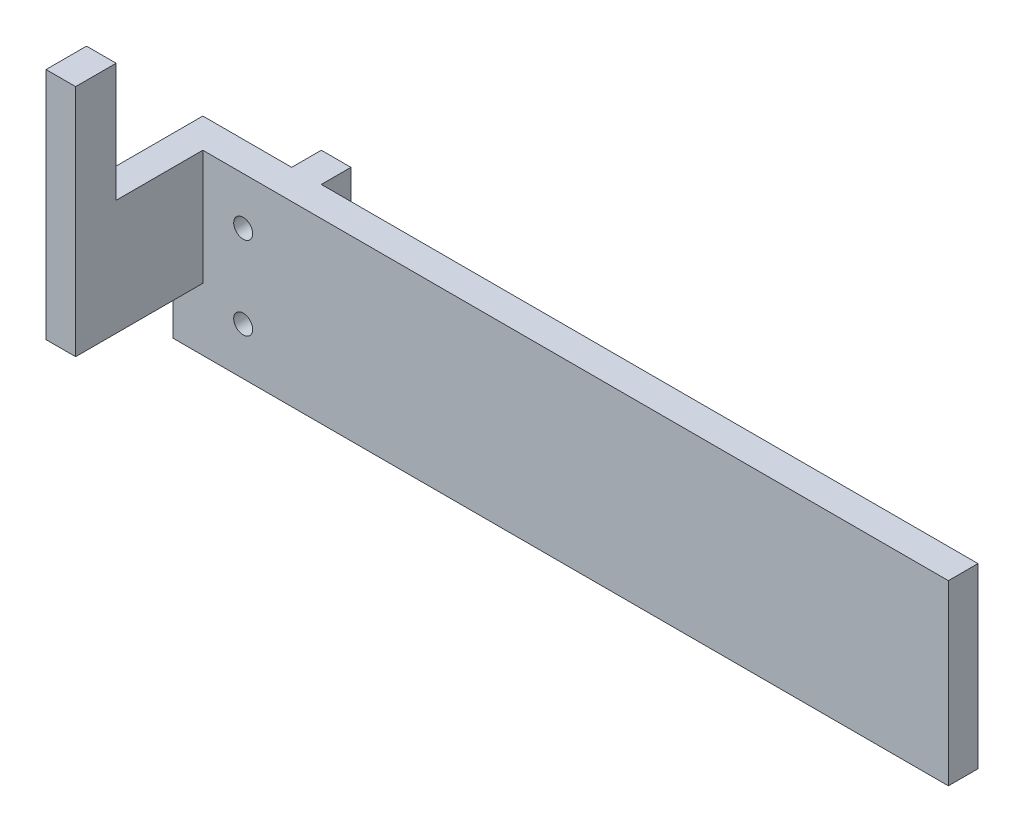
SolidWorks part; units mm, degrees
ref_plane "Front Plane" through (0, 0, 0) normal (0, 0, 1) x (1, 0, 0)
ref_plane "Top Plane" through (0, 0, 0) normal (0, 1, 0) x (1, 0, 0)
ref_plane "Right Plane" through (0, 0, 0) normal (1, 0, 0) x (0, 0, -1)
sketch "Sketch1" plane through (0, 0, 0) normal (0, 0, 1) x (1, 0, 0)
  line L0 (10, 0) -> (0, 0)
  line L1 (10, 0) -> (10, -30)
  line L2 (10, -30) -> (0, -30)
  line L3 (0, 0) -> (0, -30)
  dimension "D1" = 10
  dimension "D2" = 30
extrude "Boss-Extrude1" add sketch "Sketch1" along normal blind 5
sketch "Sketch2" plane through (0, 0, 0) normal (0, 0, -1) x (-1, 0, 0)
  line L0 (-10, 0) -> (0, 0) construction
  line L1 (-10, -30) -> (-10, 0) construction
  line L2 (0, -30) -> (-10, -30) construction
  circle A0 centre (-6.8103, -8) radius 1.6
  circle A1 centre (-6.8103, -22) radius 1.6
  dimension "D1" = 3.2
  dimension "D2" = 3.2
  dimension "D3" = 8
  dimension "D4" = 3.1897
  dimension "D5" = 8
  dimension "D6" = 3.1897
extrude "Cut-Extrude2" cut sketch "Sketch2" against normal blind 43
sketch "Sketch4" plane through (0, 0, 0) normal (0, 0, 1) x (1, 0, 0)
  line L0 (0, -30) -> (10, -30) construction
  line L1 (10, 0) -> (15, 0)
  line L2 (10, 0) -> (10, -30)
  line L3 (10, -30) -> (15, -30)
  line L4 (15, 0) -> (15, -30)
  dimension "D1" = 5
extrude "Boss-Extrude2" add sketch "Sketch4" against normal blind 5 and the other way up to surface (5 mm away)
ref_plane "Plane1" through (72.8497, 0, 0) normal (-1, 0, 0) x (0, 0, 1)
sketch "Sketch6" plane through (72.8497, 0, 0) normal (-1, 0, 0) x (0, 0, 1)
  line L0 (5, 0) -> (-5, 0) construction
  line L1 (5, -30) -> (0, -30)
  line L2 (5, -30) -> (5, 0)
  line L3 (5, 0) -> (0, 0)
  line L4 (0, -30) -> (0, 0)
  dimension "D1" = 5
extrude "Boss-Extrude4" add sketch "Sketch6" along normal up to surface and the other way up to surface
sketch "Sketch7" plane through (0, 0, 0) normal (0, 0, -1) x (-1, 0, 0)
  line L0 (0, -30) -> (0, 0)
  line L1 (0, -30) -> (5, -30)
  line L2 (0, 0) -> (5, 0)
  line L3 (5, -30) -> (5, 0)
  line L4 (-15, -30) -> (-125.8497, -30) construction
  dimension "D1" = 5
extrude "Boss-Extrude5" add sketch "Sketch7" against normal up to surface (26.4729 mm away)
sketch "Sketch8" plane through (0, 0, 0) normal (0, 1, 0) x (1, 0, 0)
  line L0 (-5, -26.4729) -> (0, -26.4729)
  line L1 (-5, -26.4729) -> (-5, -19.6342)
  line L2 (0, -26.4729) -> (0, -19.6342)
  line L3 (-5, -19.6342) -> (0, -19.6342)
  line L4 (-5, -26.4729) -> (-5, 0) construction
extrude "Boss-Extrude6" add sketch "Sketch8" along normal up to surface (20.0348 mm away)
ref_plane "Plane2" through (0, -19.456, 0) normal (0, -1, 0) x (-1, 0, 0)
sketch "Sketch9" plane through (0, -19.456, 0) normal (0, -1, 0) x (1, 0, 0)
  line L0 (-5, 26.4729) -> (0, 26.4729)
  line L1 (-5, 26.4729) -> (-5, 5)
  line L2 (0, 26.4729) -> (0, 5)
  line L3 (-5, 5) -> (0, 5)
  line L4 (-5, 26.4729) -> (-5, 0) construction
  line L5 (0, 26.4729) -> (0, 5) construction
  line L6 (0, 5) -> (125.8497, 5) construction
  line L7 (0, 26.4729) -> (-5, 26.4729) construction
  point P10 (-2.5, 26.4729)
extrude "Cut-Extrude3" cut sketch "Sketch9" along normal through all
